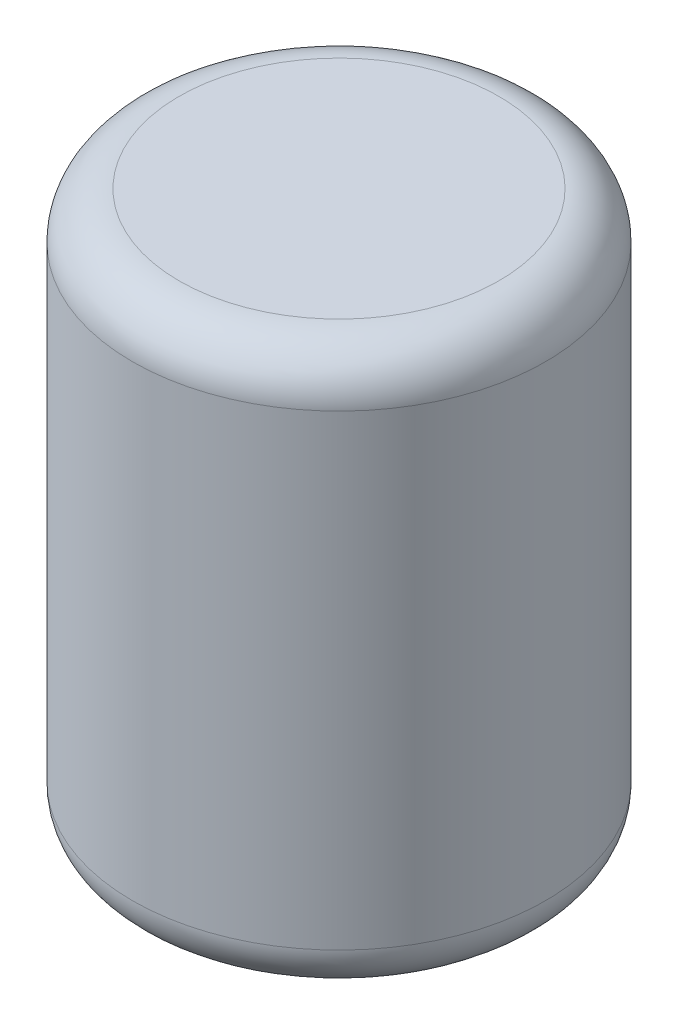
SolidWorks part; units mm, degrees
material "Natural Rubber"
ref_plane "Front" through (0, 0, 0) normal (0, 0, 1) x (1, 0, 0)
ref_plane "Top" through (0, 0, 0) normal (0, 1, 0) x (1, 0, 0)
ref_plane "Right" through (0, 0, 0) normal (1, 0, 0) x (0, 0, -1)
sketch "Sketch2" plane through (0, 0, 0) normal (0, 1, 0) x (1, 0, 0)
  circle A0 centre (0, 0) radius 44.25
  dimension "D1" = 88.5
extrude "Boss-Extrude1" add sketch "Sketch2" along normal blind 120
fillet "Fillet1" radius 10 2 edges at (0, 120, 44.25) (0, 0, 44.25)
